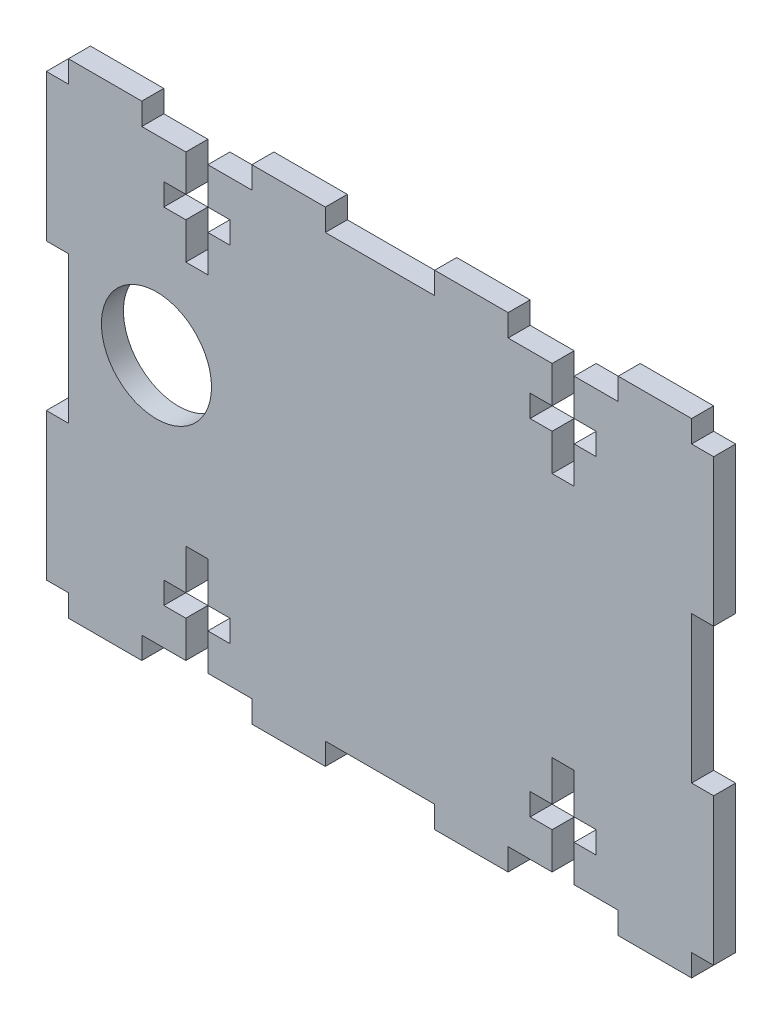
SolidWorks part; units mm, degrees
ref_plane "Front Plane" through (0, 0, 0) normal (0, 0, 1) x (1, 0, 0)
ref_plane "Top Plane" through (0, 0, 0) normal (0, 1, 0) x (1, 0, 0)
ref_plane "Right Plane" through (0, 0, 0) normal (1, 0, 0) x (0, 0, -1)
sketch "Model" plane through (0, 0, 0) normal (0, 0, 1) x (1, 0, 0)
  line L0 (21, -151.1997) -> (18, -151.1997)
  line L1 (24, -151.1997) -> (27, -151.1997)
  line L2 (18, -151.1997) -> (18, -148.1997)
  line L3 (27, -151.1997) -> (27, -148.1997)
  line L4 (5, -96.1997) -> (2, -96.1997)
  line L5 (5, -93.1997) -> (5, -96.1997)
  line L6 (15, -93.1997) -> (5, -93.1997)
  line L7 (15, -96.1997) -> (15, -93.1997)
  line L8 (21, -96.1997) -> (15, -96.1997)
  line L9 (21, -96.1997) -> (21, -101.1997)
  line L10 (21, -101.1997) -> (18, -101.1997)
  line L11 (18, -101.1997) -> (18, -104.1964)
  line L12 (18, -104.1964) -> (21, -104.1964)
  line L13 (21, -104.1964) -> (21, -109.1964)
  line L14 (21, -109.1964) -> (24, -109.1964)
  line L15 (24, -109.1964) -> (24, -104.1964)
  line L16 (24, -104.1964) -> (27, -104.1964)
  line L17 (27, -104.1964) -> (27, -101.1997)
  line L18 (27, -101.1997) -> (24, -101.1997)
  line L19 (24, -101.1997) -> (24, -96.1997)
  line L20 (30, -96.1997) -> (24, -96.1997)
  line L21 (30, -93.1997) -> (30, -96.1997)
  line L22 (40, -93.1997) -> (30, -93.1997)
  line L23 (40, -96.1997) -> (40, -93.1997)
  line L24 (54.9, -96.1997) -> (40, -96.1997)
  line L25 (54.9, -93.1997) -> (54.9, -96.1997)
  line L26 (64.9, -93.1997) -> (54.9, -93.1997)
  line L27 (64.9, -96.1997) -> (64.9, -93.1997)
  line L28 (70.9, -96.1997) -> (64.9, -96.1997)
  line L29 (70.9, -96.1997) -> (70.9, -101.1997)
  line L30 (70.9, -101.1997) -> (67.9, -101.1997)
  line L31 (67.9, -101.1997) -> (67.9, -104.1964)
  line L32 (67.9, -104.1964) -> (70.9, -104.1964)
  line L33 (70.9, -104.1964) -> (70.9, -109.1964)
  line L34 (70.9, -109.1964) -> (73.9, -109.1964)
  line L35 (73.9, -109.1964) -> (73.9, -104.1964)
  line L36 (73.9, -104.1964) -> (76.9, -104.1964)
  line L37 (76.9, -104.1964) -> (76.9, -101.1997)
  line L38 (76.9, -101.1997) -> (73.9, -101.1997)
  line L39 (73.9, -101.1997) -> (73.9, -96.1997)
  line L40 (79.9, -96.1997) -> (73.9, -96.1997)
  line L41 (79.9, -93.1997) -> (79.9, -96.1997)
  line L42 (89.9, -93.1997) -> (79.9, -93.1997)
  line L43 (89.9, -96.1997) -> (89.9, -93.1997)
  line L44 (92.9, -96.1997) -> (89.9, -96.1997)
  line L45 (92.9, -116.1997) -> (92.9, -96.1997)
  line L46 (89.9, -116.1997) -> (92.9, -116.1997)
  line L47 (89.9, -136.1997) -> (89.9, -116.1997)
  line L48 (92.9, -136.1997) -> (89.9, -136.1997)
  line L49 (92.9, -156.1997) -> (92.9, -136.1997)
  line L50 (89.9, -156.1997) -> (92.9, -156.1997)
  line L51 (89.9, -159.1997) -> (89.9, -156.1997)
  line L52 (79.9, -159.1997) -> (89.9, -159.1997)
  line L53 (79.9, -156.1997) -> (79.9, -159.1997)
  line L54 (73.9, -156.1997) -> (79.9, -156.1997)
  line L55 (70.9, -156.1997) -> (70.9, -151.1997)
  line L56 (70.9, -151.1997) -> (67.9, -151.1997)
  line L57 (67.9, -151.1997) -> (67.9, -148.1997)
  line L58 (67.9, -148.1997) -> (70.9, -148.1997)
  line L59 (70.9, -148.1997) -> (70.9, -142.6997)
  line L60 (70.9, -142.6997) -> (73.9, -142.6997)
  line L61 (73.9, -142.6997) -> (73.9, -148.1997)
  line L62 (73.9, -148.1997) -> (76.9, -148.1997)
  line L63 (76.9, -148.1997) -> (76.9, -151.1997)
  line L64 (76.9, -151.1997) -> (73.9, -151.1997)
  line L65 (73.9, -151.1997) -> (73.9, -156.1997)
  line L66 (64.9, -156.1997) -> (70.9, -156.1997)
  line L67 (64.9, -159.1997) -> (64.9, -156.1997)
  line L68 (54.9, -159.1997) -> (64.9, -159.1997)
  line L69 (54.9, -156.1997) -> (54.9, -159.1997)
  line L70 (40, -156.1997) -> (54.9, -156.1997)
  line L71 (40, -159.1997) -> (40, -156.1997)
  line L72 (30, -159.1997) -> (40, -159.1997)
  line L73 (30, -156.1997) -> (30, -159.1997)
  line L74 (24, -156.1997) -> (30, -156.1997)
  line L75 (24, -151.1997) -> (24, -156.1997)
  line L76 (18, -148.1997) -> (21, -148.1997)
  line L77 (27, -148.1997) -> (24, -148.1997)
  line L78 (21, -148.1997) -> (21, -142.6997)
  line L79 (24, -148.1997) -> (24, -142.6997)
  line L80 (21, -142.6997) -> (24, -142.6997)
  line L85 (21, -156.1997) -> (21, -151.1997)
  line L86 (15, -156.1997) -> (21, -156.1997)
  line L87 (15, -159.1997) -> (15, -156.1997)
  line L88 (5, -159.1997) -> (15, -159.1997)
  line L89 (5, -156.1997) -> (5, -159.1997)
  line L90 (2, -156.1997) -> (5, -156.1997)
  line L91 (2, -136.1997) -> (2, -156.1997)
  line L92 (5, -136.1997) -> (2, -136.1997)
  line L93 (5, -116.1997) -> (5, -136.1997)
  line L94 (2, -116.1997) -> (5, -116.1997)
  line L95 (2, -96.1997) -> (2, -116.1997)
  circle A0 centre (17, -122.1997) radius 7.5
  dimension "D3" = 15
  dimension "D4" = 37
  dimension "D5" = 15
  dimension "D1" = 90.9
  dimension "D2" = 84.9
  dimension "D6" = 5
  dimension "D7" = 5
  dimension "D8" = 3
  dimension "D9" = 3
  dimension "D10" = 3
  dimension "D11" = 3
  dimension "D12" = 5.5
  dimension "D13" = 5.5
  dimension "D14" = 5
  dimension "D15" = 5
  dimension "D16" = 2.9967
  dimension "D17" = 5
  dimension "D18" = 2.9967
  dimension "D19" = 5
  dimension "D20" = 3
extrude "Boss-Extrude1" add sketch "Model" along normal blind 3 contours L93 L92 L91 L90 L89 L88 L87 L86 L85 L0 L2 L76 L78 L80 L79 L77 L3 L1 L75 L74 L73 L72 L71 L70 L69 L68 L67 L66 L55 L56 L57 L58 L59 L60 L61 L62 L63 L64 L65 L54 L53 L52 L51 L50 L49 L48 L47 L46 L45 L44 L43 L42 L41 L40 L39 L38 L37 L36 L35 L34 L33 L32 L31 L30 L29 L28 L27 L26 L25 L24 L23 L22 L21 L20 L19 L18 L17 L16 L15 L14 L13 L12 L11 L10 L9 L8 L7 L6 L5 L4 L95 L94 | A0
